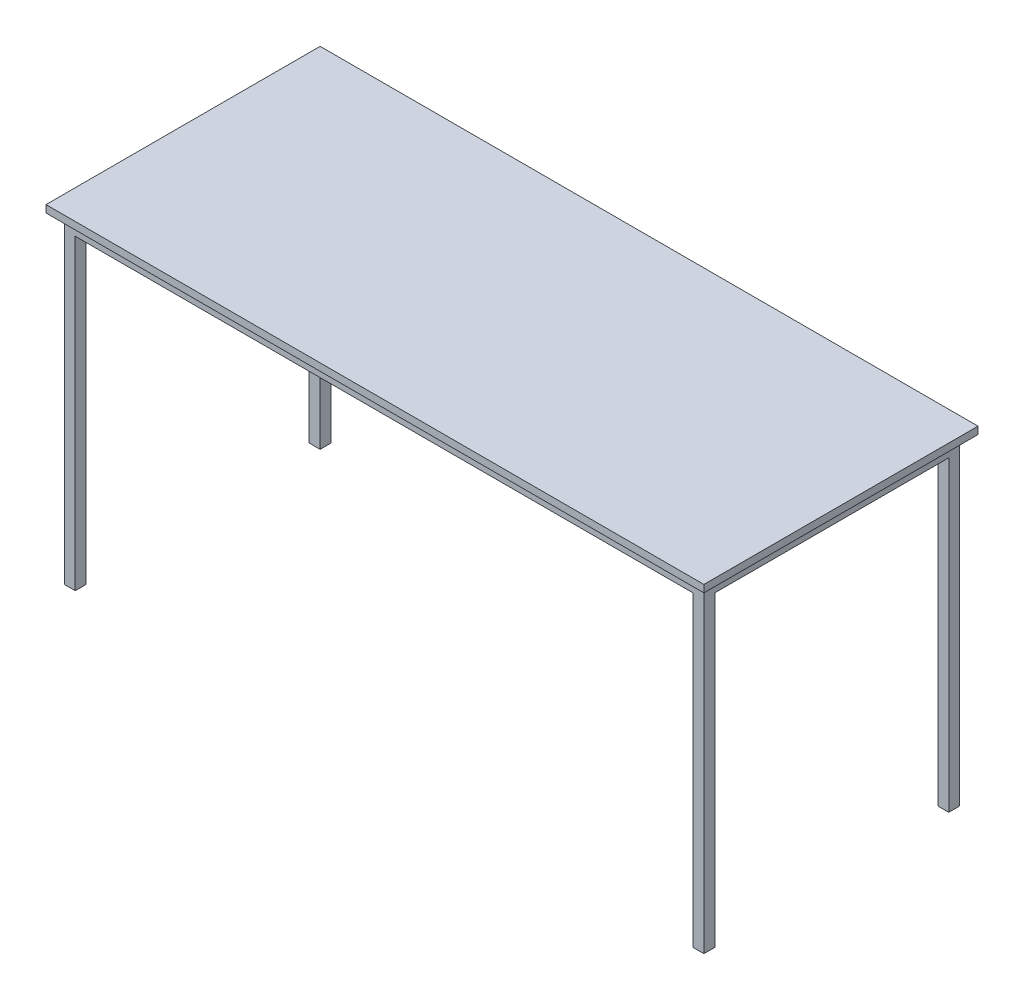
SolidWorks part; units mm, degrees
ref_plane "Front Plane" through (0, 0, 0) normal (0, 0, 1) x (1, 0, 0)
ref_plane "Top Plane" through (0, 0, 0) normal (0, 1, 0) x (1, 0, 0)
ref_plane "Right Plane" through (0, 0, 0) normal (1, 0, 0) x (0, 0, -1)
sketch "Sketch1" plane through (0, 0, 0) normal (0, 1, 0) x (1, 0, 0)
  line L1 (0, 0) -> (1750, 0)
  line L2 (0, 0) -> (0, 700)
  line L3 (0, 700) -> (1750, 700)
  line L4 (1750, 0) -> (1750, 700)
extrude "Extrude-Thin1" add sketch "Sketch1" against normal blind 40 thin thin type one direction reverse wall 30
sketch "Sketch2" plane through (0, 0, 0) normal (0, 1, 0) x (1, 0, 0)
  line L1 (0, 700) -> (30, 700)
  line L2 (0, 700) -> (0, 670)
  line L3 (0, 670) -> (30, 670)
  line L4 (30, 700) -> (30, 670)
  line L5 (0, 0) -> (30, 0)
  line L6 (0, 0) -> (0, 30)
  line L7 (0, 30) -> (30, 30)
  line L8 (30, 0) -> (30, 30)
  line L9 (1750, 0) -> (1720, 0)
  line L10 (1750, 0) -> (1750, 30)
  line L11 (1750, 30) -> (1720, 30)
  line L12 (1720, 0) -> (1720, 30)
  line L13 (1750, 700) -> (1720, 700)
  line L14 (1750, 700) -> (1750, 670)
  line L15 (1750, 670) -> (1720, 670)
  line L16 (1720, 700) -> (1720, 670)
extrude "Boss-Extrude1" add sketch "Sketch2" against normal blind 880
sketch "Sketch3" plane through (0, 0, 0) normal (0, 1, 0) x (1, 0, 0)
  line L5 (-25, 725) -> (1775, 725)
  line L6 (-25, 725) -> (-25, -25)
  line L7 (-25, -25) -> (1775, -25)
  line L8 (1775, 725) -> (1775, -25)
extrude "Boss-Extrude2" add sketch "Sketch3" along normal blind 20 separate body
